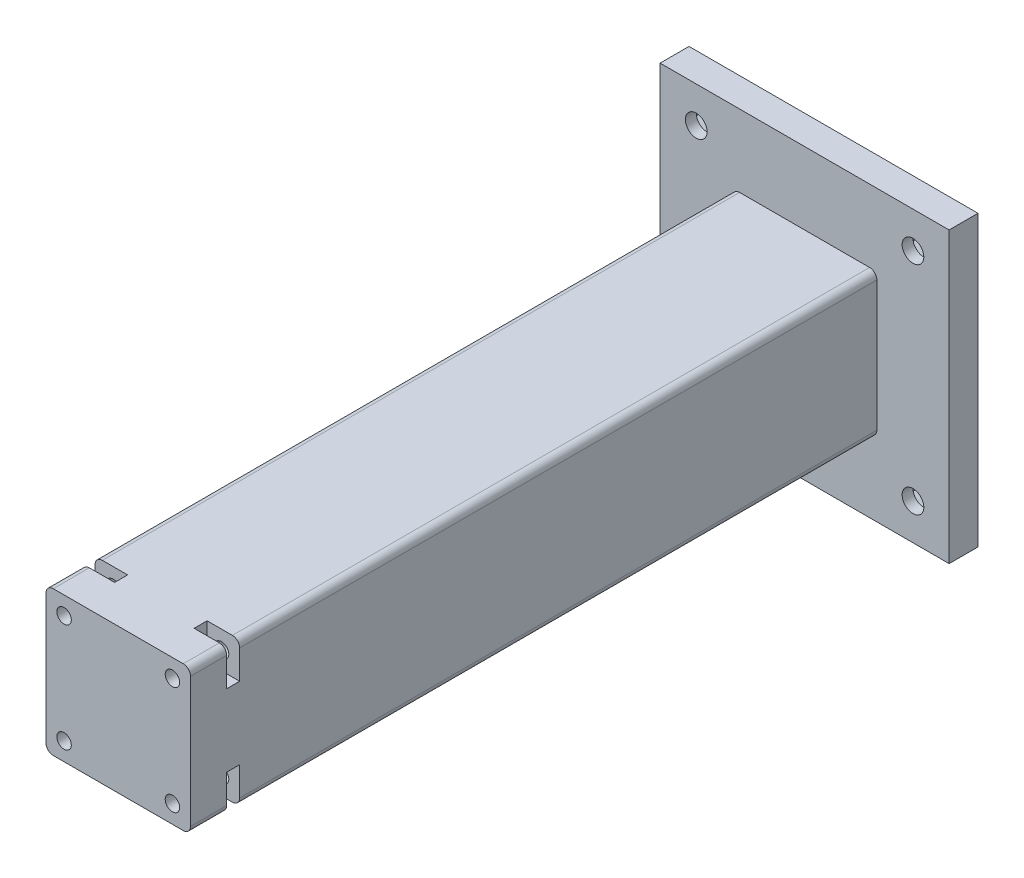
SolidWorks part; units mm, degrees
ref_plane "Plan de face" through (0, 0, 0) normal (0, 0, 1) x (1, 0, 0)
ref_plane "Plan de dessus" through (0, 0, 0) normal (0, 1, 0) x (1, 0, 0)
ref_plane "Plan de droite" through (0, 0, 0) normal (1, 0, 0) x (0, 0, -1)
sketch "Esquisse1" plane through (0, 0, 0) normal (0, 0, 1) x (1, 0, 0)
  line L1 (-20, 20) -> (20, 20)
  line L2 (-20, 20) -> (-20, -20)
  line L3 (-20, -20) -> (20, -20)
  line L4 (20, 20) -> (20, -20)
  dimension "D1" = 20
  dimension "D2" = 40
  dimension "D3" = 20
  dimension "D4" = 40
extrude "Boss.-Extru.1" add sketch "Esquisse1" along normal blind 4
sketch "Esquisse4" plane through (0, 0, 4) normal (0, 0, 1) x (1, 0, 0)
  line L1 (-10, 10) -> (10, 10)
  line L2 (-10, 10) -> (-10, -10)
  line L3 (-10, -10) -> (10, -10)
  line L4 (10, 10) -> (10, -10)
  point P4 (0, 0)
  dimension "D1" = 10
  dimension "D2" = 20
  dimension "D3" = 10
  dimension "D4" = 20
extrude "Boss.-Extru.4" add sketch "Esquisse4" along normal blind 95
fillet "Congé3" radius 1 4 edges at (-10, 10, 51.5) (10, 10, 51.5) (-10, -10, 51.5) (10, -10, 51.5)
sketch "Esquisse5" plane through (0, 0, 99) normal (0, 0, 1) x (1, 0, 0)
  line L0 (9, 10) -> (-9, 10) construction
  line L1 (-10, 9) -> (-10, -9) construction
  line L2 (10, -9) -> (10, 9) construction
  line L3 (-9, -10) -> (9, -10) construction
  circle A0 centre (7.5, 7.5) radius 1
  circle A1 centre (-7.5, 7.5) radius 1
  circle A2 centre (-7.5, -7.5) radius 1
  circle A3 centre (7.5, -7.5) radius 1
  dimension "D1" = 2
  dimension "D2" = 2.5
  dimension "D3" = 2.5
  dimension "D4" = 2.5
  dimension "D5" = 2.5
extrude "Enlèv. mat.-Extru.1" cut sketch "Esquisse5" against normal blind 20
sketch "Esquisse6" plane through (0, -10, 0) normal (0, -1, 0) x (1, 0, 0)
  line L0 (-9, 99) -> (9, 99) construction
  line L1 (-10, 94) -> (-5.5, 94)
  line L2 (-10, 94) -> (-10, 92.2)
  line L3 (-10, 92.2) -> (-5.5, 92.2)
  line L4 (-5.5, 94) -> (-5.5, 92.2)
  line L5 (10, 94) -> (5.5, 94)
  line L6 (10, 94) -> (10, 92.2)
  line L7 (10, 92.2) -> (5.5, 92.2)
  line L8 (5.5, 94) -> (5.5, 92.2)
  line L9 (-10, 4) -> (-10, 99) construction
  line L10 (10, 99) -> (10, 4) construction
  dimension "D2" = 5
  dimension "D3" = 1.8
  dimension "D5" = 4.5
  dimension "D6" = 4.5
extrude "Enlèv. mat.-Extru.2" cut sketch "Esquisse6" against normal blind 5
mirror "Symétrie1" about plane through (0, 0, 0) normal (0, 1, 0) of "Enlèv. mat.-Extru.2"
sketch "Esquisse7" plane through (0, 0, 0) normal (0, 0, -1) x (-1, 0, 0)
  line L0 (20, 20) -> (20, -20) construction
  line L1 (-20, -20) -> (-20, 20) construction
  line L2 (20, -20) -> (-20, -20) construction
  line L3 (-20, 20) -> (20, 20) construction
  line L4 (-9, 10) -> (9, 10) construction
  line L5 (10, 9) -> (10, -9) construction
  circle A0 centre (15, 15) radius 1.5
  circle A1 centre (15, -15) radius 1.5
  circle A2 centre (-15, -15) radius 1.5
  circle A3 centre (-15, 15) radius 1.5
  dimension "D1" = 3
  dimension "D2" = 5
  dimension "D3" = 5
  dimension "D4" = 5
  dimension "D5" = 5
  dimension "D6" = 5
  dimension "D7" = 5
extrude "Enlèv. mat.-Extru.3" cut sketch "Esquisse7" against normal up to surface (4 mm away) up to face at (0, 0, 4)
sketch "Esquisse8" plane through (0, 0, 0) normal (0, 0, -1) x (-1, 0, 0)
  line L0 (-20, -20) -> (-20, 20) construction
  line L1 (-12.2287, 13.4) -> (-12.2287, 16.6)
  line L2 (-12.2287, 16.6) -> (-15, 18.2)
  line L3 (-15, 18.2) -> (-17.7713, 16.6)
  line L4 (-17.7713, 16.6) -> (-17.7713, 13.4)
  line L5 (-17.7713, 13.4) -> (-15, 11.8)
  line L6 (-15, 11.8) -> (-12.2287, 13.4)
  line L7 (15, 11.8) -> (17.7713, 13.4)
  line L8 (17.7713, 13.4) -> (17.7713, 16.6)
  line L9 (17.7713, 16.6) -> (15, 18.2)
  line L10 (15, 18.2) -> (12.2287, 16.6)
  line L11 (12.2287, 16.6) -> (12.2287, 13.4)
  line L12 (12.2287, 13.4) -> (15, 11.8)
  line L13 (15, -18.2) -> (17.7713, -16.6)
  line L14 (17.7713, -16.6) -> (17.7713, -13.4)
  line L15 (17.7713, -13.4) -> (15, -11.8)
  line L16 (15, -11.8) -> (12.2287, -13.4)
  line L17 (12.2287, -13.4) -> (12.2287, -16.6)
  line L18 (12.2287, -16.6) -> (15, -18.2)
  line L19 (-12.2287, -16.6) -> (-12.2287, -13.4)
  line L20 (-12.2287, -13.4) -> (-15, -11.8)
  line L21 (-15, -11.8) -> (-17.7713, -13.4)
  line L22 (-17.7713, -13.4) -> (-17.7713, -16.6)
  line L23 (-17.7713, -16.6) -> (-15, -18.2)
  line L24 (-15, -18.2) -> (-12.2287, -16.6)
  line L25 (20, 20) -> (20, -20) construction
  circle A0 centre (-15, 15) radius 2.7713 construction
  circle A1 centre (15, 15) radius 2.7713 construction
  circle A2 centre (15, -15) radius 2.7713 construction
  circle A3 centre (-15, -15) radius 2.7713 construction
  dimension "D1" = 3.2
  dimension "D2" = 3.2
  dimension "D3" = 3.2
  dimension "D4" = 3.2
extrude "Enlèv. mat.-Extru.4" cut sketch "Esquisse8" against normal blind 2.5
